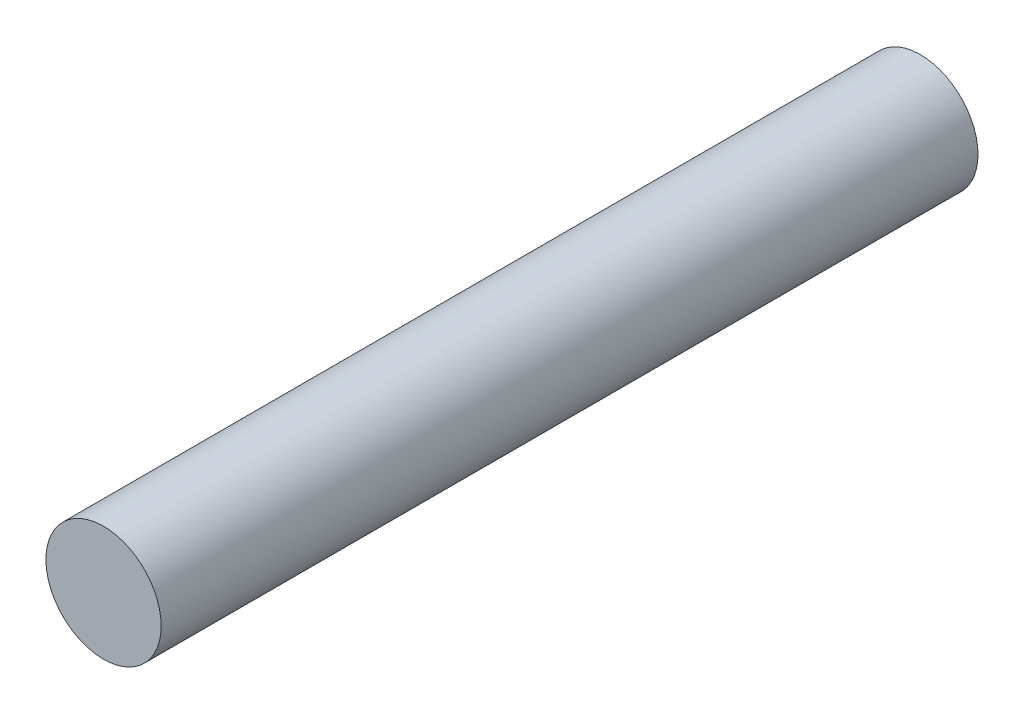
SolidWorks part; units mm, degrees
material "Balsa"
ref_plane "Front Plane" through (0, 0, 0) normal (0, 0, 1) x (1, 0, 0)
ref_plane "Top Plane" through (0, 0, 0) normal (0, 1, 0) x (1, 0, 0)
ref_plane "Right Plane" through (0, 0, 0) normal (1, 0, 0) x (0, 0, -1)
sketch "Sketch1" plane through (0, 0, 0) normal (0, 0, 1) x (1, 0, 0)
  circle A0 centre (0, 0) radius 3.175
  dimension "D1" = 6.35
extrude "Boss-Extrude1" add sketch "Sketch1" along normal blind 45
